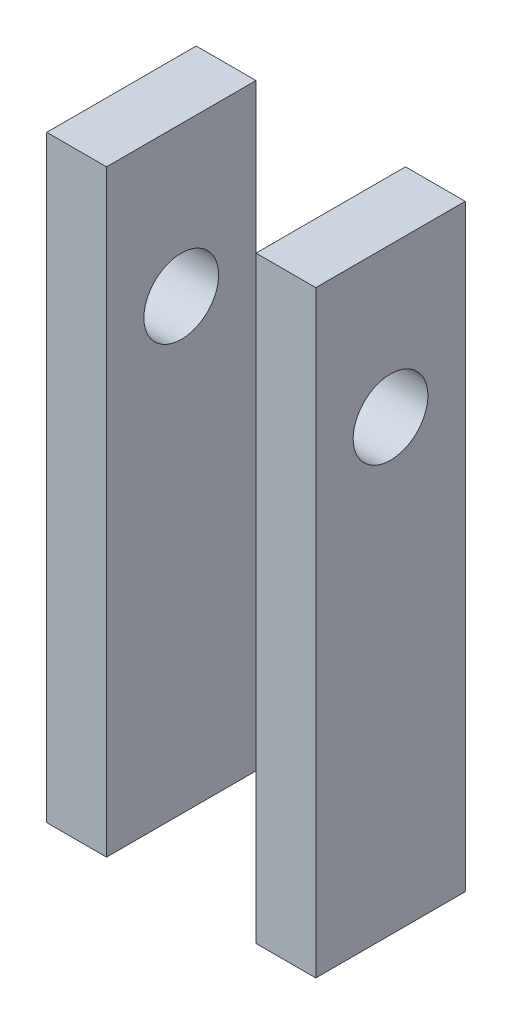
SolidWorks part; units mm, degrees
ref_plane "Front Plane" through (0, 0, 0) normal (0, 0, 1) x (1, 0, 0)
ref_plane "Top Plane" through (0, 0, 0) normal (0, 1, 0) x (1, 0, 0)
ref_plane "Right Plane" through (0, 0, 0) normal (1, 0, 0) x (0, 0, -1)
sketch "Sketch1" plane through (0, 0, 0) normal (0, 1, 0) x (1, 0, 0)
  line L1 (-11.43, -6.35) -> (11.43, -6.35)
  line L2 (-11.43, -6.35) -> (-11.43, 6.35)
  line L3 (-11.43, 6.35) -> (11.43, 6.35)
  line L4 (11.43, -6.35) -> (11.43, 6.35)
  line L5 (-11.43, -6.35) -> (11.43, 6.35) construction
  line L6 (-11.43, 6.35) -> (11.43, -6.35) construction
  line L7 (-6.35, -6.35) -> (6.35, -6.35)
  line L8 (-6.35, -6.35) -> (-6.35, 6.35)
  line L9 (-6.35, 6.35) -> (6.35, 6.35)
  line L10 (6.35, -6.35) -> (6.35, 6.35)
  line L11 (-6.35, -6.35) -> (6.35, 6.35) construction
  line L12 (-6.35, 6.35) -> (6.35, -6.35) construction
  point P0 (0, 0)
  point P6 (0, 0)
  dimension "D1" = 22.86
  dimension "D2" = 12.7
  dimension "D3" = 12.7
extrude "Boss-Extrude1" add sketch "Sketch1" along normal blind 50.8 contours L1 L8 L3 L2 | L10 L1 L4 L3
sketch "Sketch2" plane through (-11.43, 0, 0) normal (-1, 0, 0) x (0, 0, 1)
  line L0 (6.35, 0) -> (-6.35, 0) construction
  circle A0 centre (0, 38.1) radius 3.175
  point P2 (0, 43.6537)
  dimension "D1" = 6.35
  dimension "D2" = 38.1
extrude "Cut-Extrude1" cut sketch "Sketch2" against normal through all
